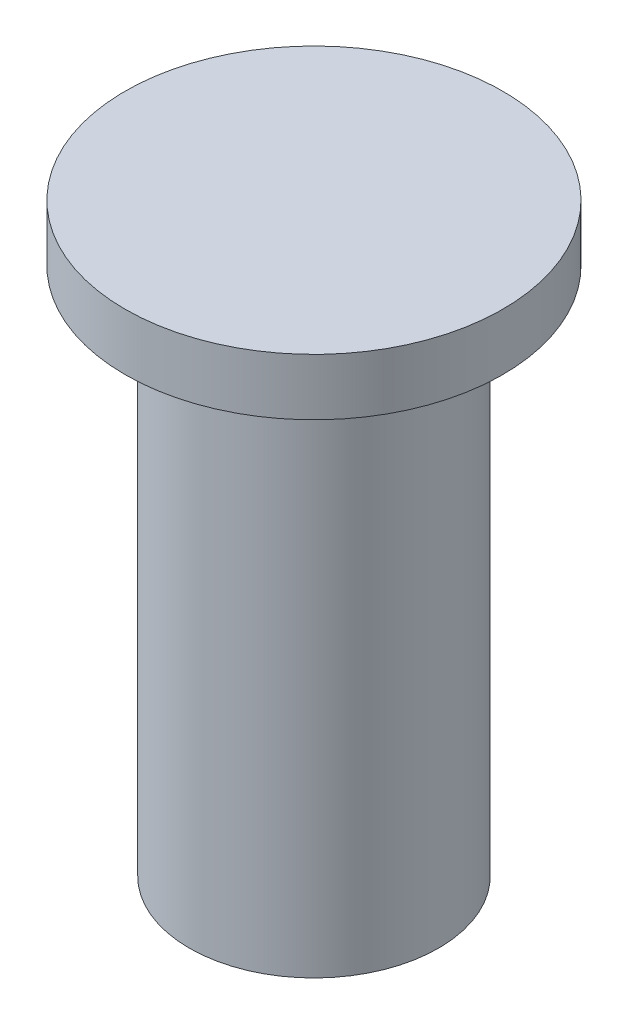
SolidWorks part; units mm, degrees
ref_plane "Front Plane" through (0, 0, 0) normal (0, 0, 1) x (1, 0, 0)
ref_plane "Top Plane" through (0, 0, 0) normal (0, 1, 0) x (1, 0, 0)
ref_plane "Right Plane" through (0, 0, 0) normal (1, 0, 0) x (0, 0, -1)
sketch "Sketch1" plane through (0, 0, 0) normal (0, 1, 0) x (1, 0, 0)
  circle A0 centre (0, 0) radius 3.3
  dimension "D1" = 6.6
extrude "Boss-Extrude1" add sketch "Sketch1" along normal blind 14
sketch "Sketch2" plane through (0, 14, 0) normal (0, 1, 0) x (1, 0, 0)
  circle A0 centre (0, 0) radius 5
extrude "Boss-Extrude2" add sketch "Sketch2" along normal blind 1.5
